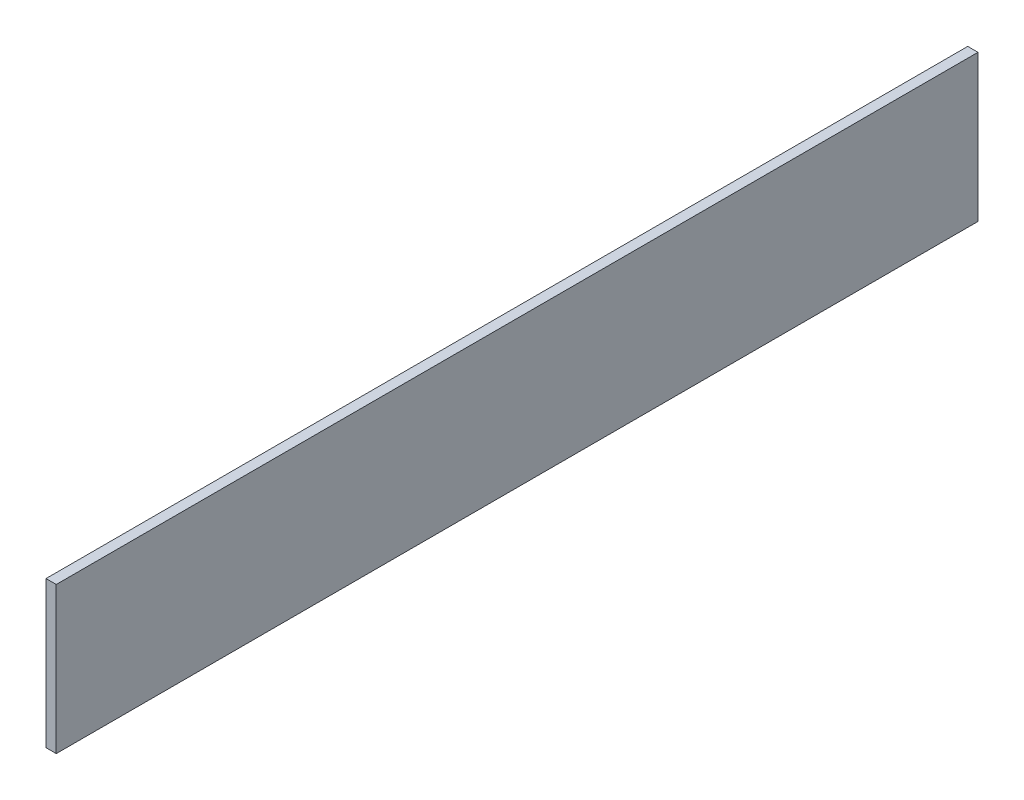
SolidWorks part; units mm, degrees
ref_plane "Ebene vorne" through (0, 0, 0) normal (0, 0, 1) x (1, 0, 0)
ref_plane "Ebene oben" through (0, 0, 0) normal (0, 1, 0) x (1, 0, 0)
ref_plane "Ebene rechts" through (0, 0, 0) normal (1, 0, 0) x (0, 0, -1)
sketch "Skizze1" plane through (0, 0, 0) normal (0, 0, 1) x (1, 0, 0)
  line L0 (97.5, 254.0237) -> (92.5, 254.0237)
  line L1 (97.5, 182.5) -> (92.5, 182.5)
  line L28 (92.5, 254.0237) -> (92.5, 182.5)
  line L29 (97.5, 182.5) -> (97.5, 254.0237)
extrude "Aufsatz-Linear austragen1" add sketch "Skizze1" along normal blind 450
